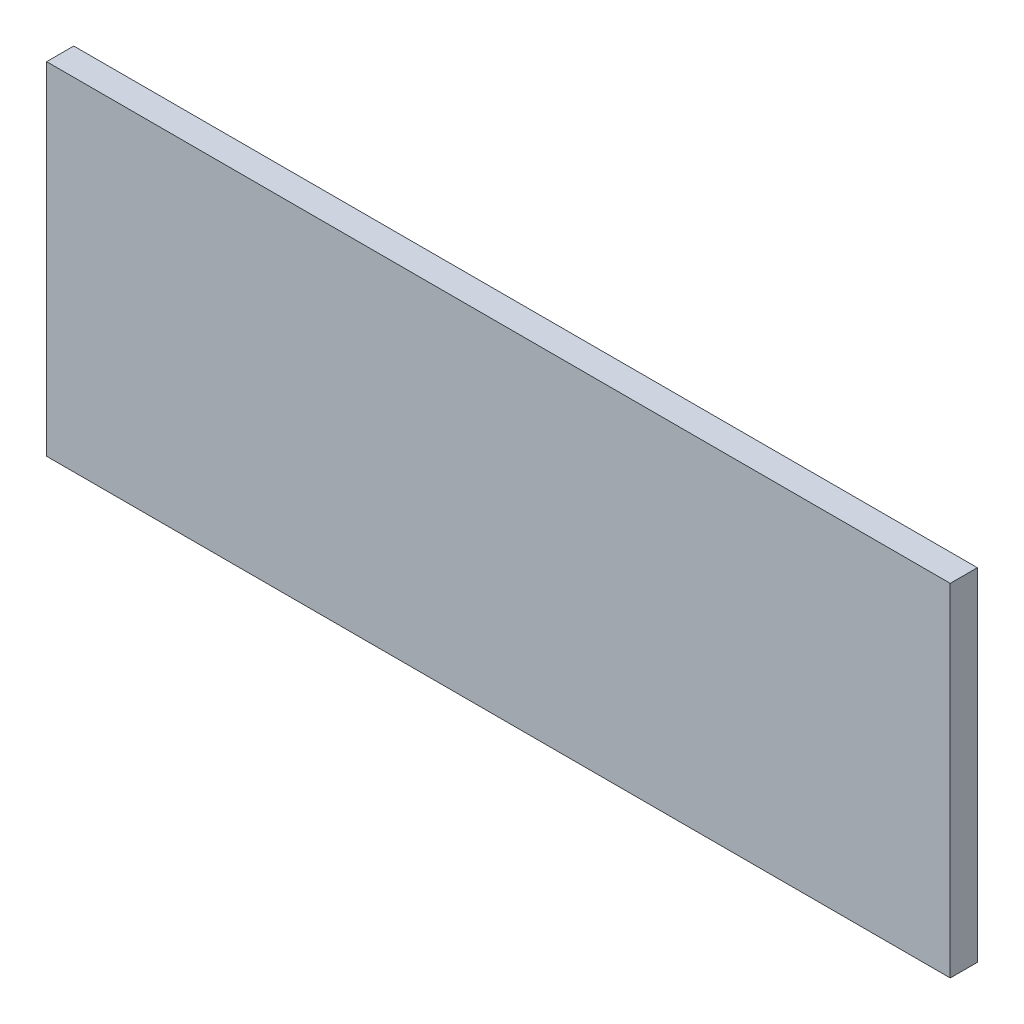
SolidWorks part; units mm, degrees
ref_plane "Front" through (0, 0, 0) normal (0, 0, 1) x (1, 0, 0)
ref_plane "Top" through (0, 0, 0) normal (0, 1, 0) x (1, 0, 0)
ref_plane "Right" through (0, 0, 0) normal (1, 0, 0) x (0, 0, -1)
sketch "Sketch1" plane through (0, 0, 0) normal (0, 0, 1) x (1, 0, 0)
  line L1 (557.5, 210.87) -> (-557.5, 210.87)
  line L2 (557.5, 210.87) -> (557.5, -210.87)
  line L3 (557.5, -210.87) -> (-557.5, -210.87)
  line L4 (-557.5, 210.87) -> (-557.5, -210.87)
  line L5 (557.5, 210.87) -> (-557.5, -210.87) construction
  line L6 (557.5, -210.87) -> (-557.5, 210.87) construction
  point P0 (0, 0)
  dimension "D1" = 421.74
  dimension "D2" = 1115
extrude "Boss-Extrude1" add sketch "Sketch1" along normal blind 33.45
